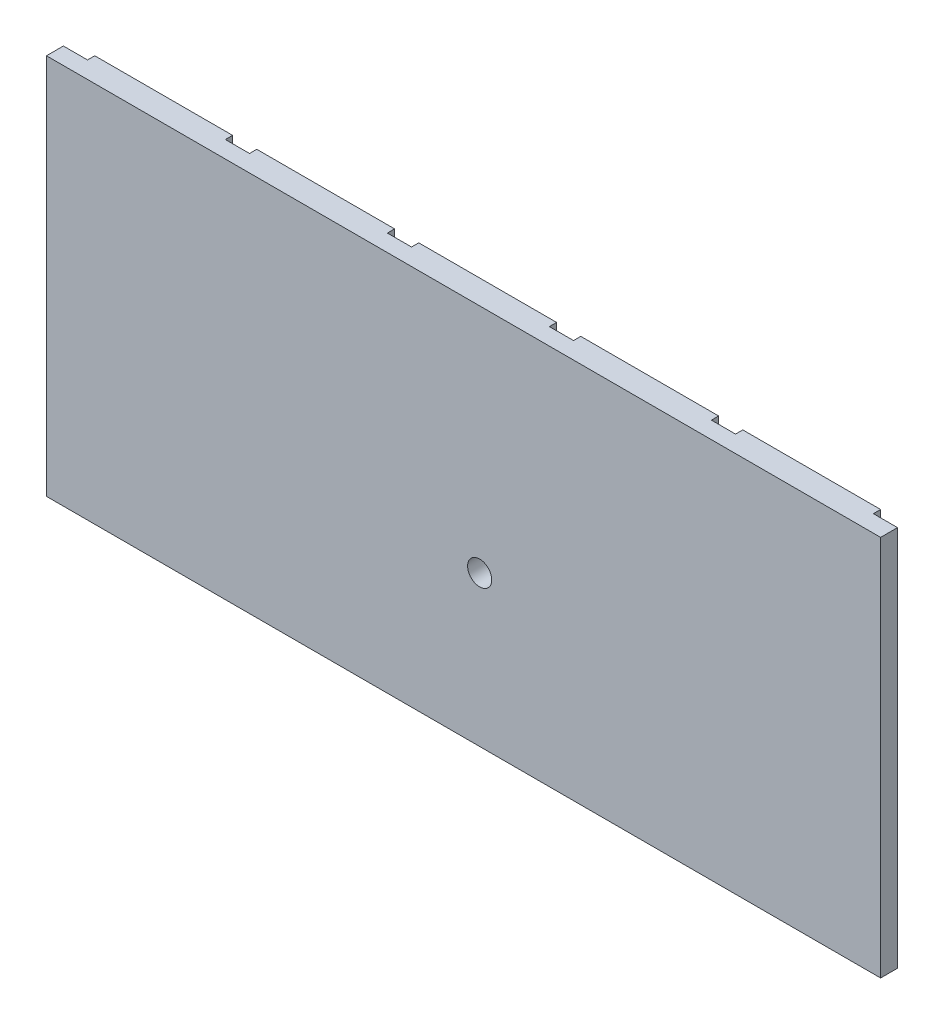
SolidWorks part; units mm, degrees
ref_plane "Front" through (0, 0, 0) normal (0, 0, 1) x (1, 0, 0)
ref_plane "Top" through (0, 0, 0) normal (0, 1, 0) x (1, 0, 0)
ref_plane "Right" through (0, 0, 0) normal (1, 0, 0) x (0, 0, -1)
sketch "Sketch1" plane through (0, 0, 0) normal (0, 0, 1) x (1, 0, 0)
  line L0 (86.3442, 0) -> (-86.3442, 0) construction
  line L1 (-86.3442, -39.5) -> (86.3442, -39.5)
  line L2 (-86.3442, -39.5) -> (-86.3442, 39.5)
  line L3 (-86.3442, 39.5) -> (86.3442, 39.5)
  line L4 (86.3442, -39.5) -> (86.3442, 39.5)
  line L5 (-86.3442, -39.5) -> (86.3442, 39.5) construction
  line L6 (-86.3442, 39.5) -> (86.3442, -39.5) construction
  line L9 (86.3442, -41) -> (86.3442, 38) construction
  circle A0 centre (3.3372, -8.3868) radius 2.5
  circle A1 centre (3.3372, -8.3868) radius 2.5 construction
  point P0 (0, 0)
extrude "Boss-Extrude1" add sketch "Sketch1" along normal blind 5
sketch "Sketch2" plane through (0, 39.5, 0) normal (0, 1, 0) x (1, 0, 0)
  line L0 (86.3442, 0) -> (-86.3442, 0) construction
  line L1 (86.3442, 0) -> (86.3442, -1.5)
  line L2 (86.3442, 0) -> (81.3442, 0)
  line L3 (86.3442, -1.5) -> (81.3442, -1.5)
  line L4 (81.3442, 0) -> (81.3442, -1.5)
  line L5 (86.3442, -5) -> (86.3442, 0) construction
  line L6 (52.8065, 0) -> (52.8065, -1.5)
  line L7 (52.8065, 0) -> (47.8065, 0)
  line L8 (52.8065, -1.5) -> (47.8065, -1.5)
  line L9 (47.8065, 0) -> (47.8065, -1.5)
  line L10 (19.2688, 0) -> (19.2688, -1.5)
  line L11 (19.2688, 0) -> (14.2688, 0)
  line L12 (19.2688, -1.5) -> (14.2688, -1.5)
  line L13 (14.2688, 0) -> (14.2688, -1.5)
  line L14 (-14.2688, 0) -> (-14.2688, -1.5)
  line L15 (-14.2688, 0) -> (-19.2688, 0)
  line L16 (-14.2688, -1.5) -> (-19.2688, -1.5)
  line L17 (-19.2688, 0) -> (-19.2688, -1.5)
  line L18 (-47.8065, 0) -> (-47.8065, -1.5)
  line L19 (-47.8065, 0) -> (-52.8065, 0)
  line L20 (-47.8065, -1.5) -> (-52.8065, -1.5)
  line L21 (-52.8065, 0) -> (-52.8065, -1.5)
  line L22 (-81.3442, 0) -> (-81.3442, -1.5)
  line L23 (-81.3442, 0) -> (-86.3442, 0)
  line L24 (-81.3442, -1.5) -> (-86.3442, -1.5)
  line L25 (-86.3442, 0) -> (-86.3442, -1.5)
  line L26 (-86.3442, -5) -> (-86.3442, 0) construction
  dimension "D1" = 1.5
  dimension "D3" = 5
  dimension "D2" = 6
extrude "Cut-Extrude1" cut sketch "Sketch2" against normal up to next
